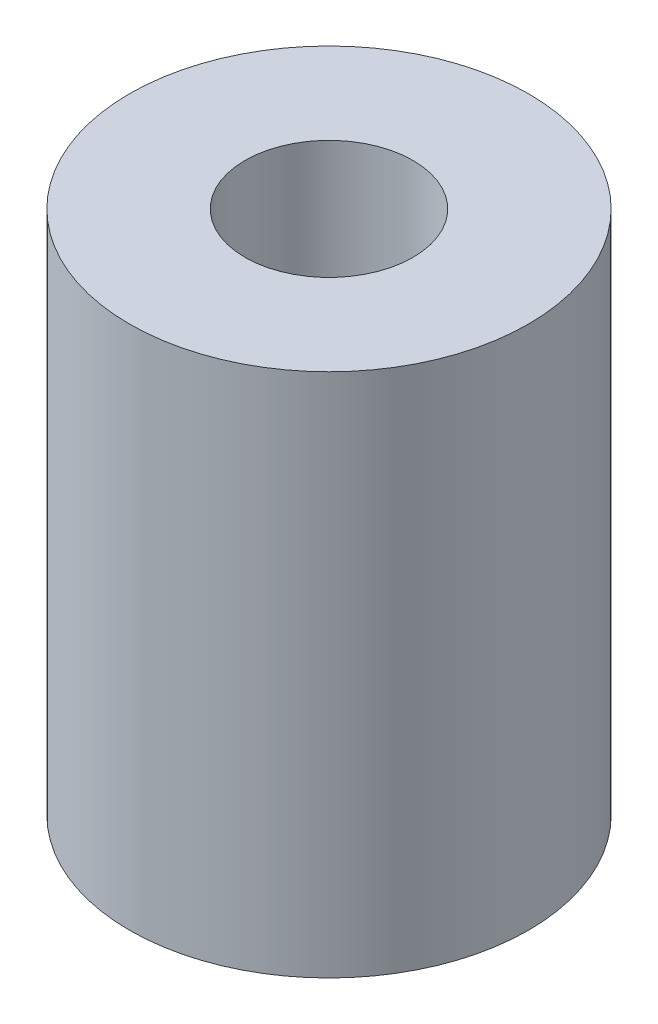
SolidWorks part; units mm, degrees
ref_plane "Plano frontal" through (0, 0, 0) normal (0, 0, 1) x (1, 0, 0)
ref_plane "Plano superior" through (0, 0, 0) normal (0, 1, 0) x (1, 0, 0)
ref_plane "Plano direito" through (0, 0, 0) normal (1, 0, 0) x (0, 0, -1)
sketch "Esboço1" plane through (0, 0, 0) normal (0, 1, 0) x (1, 0, 0)
  circle A0 centre (0, 0) radius 9.5
  dimension "D1" = 19
extrude "Ressalto-extrusão1" add sketch "Esboço1" along normal blind 25
sketch "Esboço2" plane through (0, 25, 0) normal (0, 1, 0) x (1, 0, 0)
  circle A0 centre (0, 0) radius 4
  dimension "D1" = 8
extrude "Corte-extrusão1" cut sketch "Esboço2" against normal blind 12.5
sketch "Esboço3" plane through (0, 0, 0) normal (0, -1, 0) x (-1, 0, 0)
  circle A0 centre (0, 0) radius 2.5
  dimension "D1" = 5
extrude "Corte-extrusão2" cut sketch "Esboço3" against normal blind 12.5
